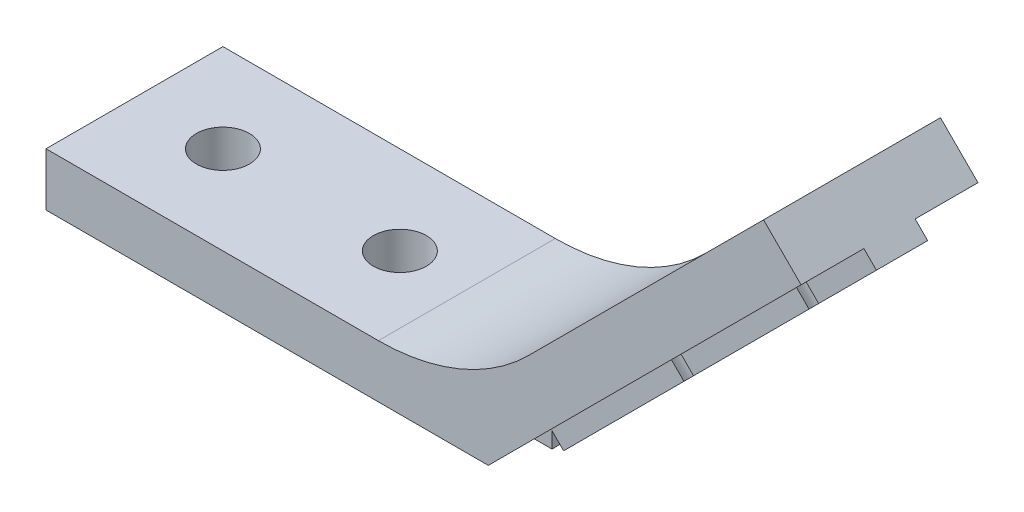
SolidWorks part; units mm, degrees
ref_plane "Front Plane" through (0, 0, 0) normal (0, 0, 1) x (1, 0, 0)
ref_plane "Top Plane" through (0, 0, 0) normal (0, 1, 0) x (1, 0, 0)
ref_plane "Right Plane" through (0, 0, 0) normal (1, 0, 0) x (0, 0, -1)
sketch "Esquisse1" plane through (0, 0, 0) normal (0, 0, 1) x (1, 0, 0)
  line L0 (-25, 0) -> (0, 0)
  line L1 (0, 0) -> (17.6777, 17.6777)
  line L2 (17.6777, 17.6777) -> (15.5563, 19.799)
  line L3 (15.5563, 19.799) -> (2.2721, 6.5147)
  line L4 (-6.2132, 3) -> (-25, 3)
  line L5 (-25, 3) -> (-25, 0)
  arc A0 (2.2721, 6.5147) -> (-6.2132, 3) centre (-6.2132, 15) cw
  dimension "D4" = 12
  dimension "D1" = 25
  dimension "D2" = 3
  dimension "D3" = 135
extrude "Boss.-Extru.1" add sketch "Esquisse1" along normal blind 10
sketch "Esquisse4" plane through (0, 0, 0) normal (0, -1, 0) x (-1, 0, 0)
  line L0 (0, -10) -> (0, 0) construction
  line L1 (0, -6.4) -> (25, -6.4)
  line L2 (0, -6.4) -> (0, -3.6)
  line L3 (0, -3.6) -> (25, -3.6)
  line L4 (25, -6.4) -> (25, -3.6)
  line L5 (25, -10) -> (25, 0) construction
  point P8 (0, -5)
  point P9 (0, -5)
  dimension "D1" = 2.8
extrude "Boss.-Extru.2" add sketch "Esquisse4" along normal blind 1
sketch "Esquisse2" plane through (0, 0, 0) normal (0, -1, 0) x (1, 0, 0)
  line L0 (-25, 10) -> (-25, 6.4) construction
  line L1 (-25, 6.4) -> (-25, 3.6) construction
  circle A0 centre (-20, 5) radius 1.5
  circle A1 centre (-10, 5) radius 1.5
  point P10 (-25, 5)
  dimension "D1" = 3
  dimension "D2" = 5
  dimension "D3" = 10
extrude "Enlèv. mat.-Extru.1" cut sketch "Esquisse2" against normal through all both and the other way through all
sketch "Esquisse5" plane through (0, 0, 0) normal (0.7071, -0.7071, 0) x (0, 0, -1)
  line L0 (-10, 25) -> (0, 25) construction
  line L1 (-6.45, 25) -> (-3.55, 25)
  line L2 (-6.45, 25) -> (-6.45, 0)
  line L3 (-6.45, 0) -> (-3.55, 0)
  line L4 (-3.55, 25) -> (-3.55, 0)
  line L5 (-3.6, 0) -> (0, 0) construction
  point P8 (-5, 25)
  point P9 (-5, 25)
  dimension "D1" = 2.9
extrude "Boss.-Extru.3" add sketch "Esquisse5" along normal blind 1
sketch "Esquisse3" plane through (0, 0, 0) normal (0.7071, -0.7071, 0) x (0, 0, -1)
  line L0 (-10, 25) -> (-6.45, 25) construction
  line L1 (-3.55, 25) -> (-6.45, 25) construction
  circle A0 centre (-5, 10) radius 1.5
  circle A1 centre (-5, 20) radius 1.5
  point P9 (-5, 25)
  dimension "D1" = 3
  dimension "D2" = 5
  dimension "D3" = 10
extrude "Enlèv. mat.-Extru.2" cut sketch "Esquisse3" against normal through all both and the other way through all
